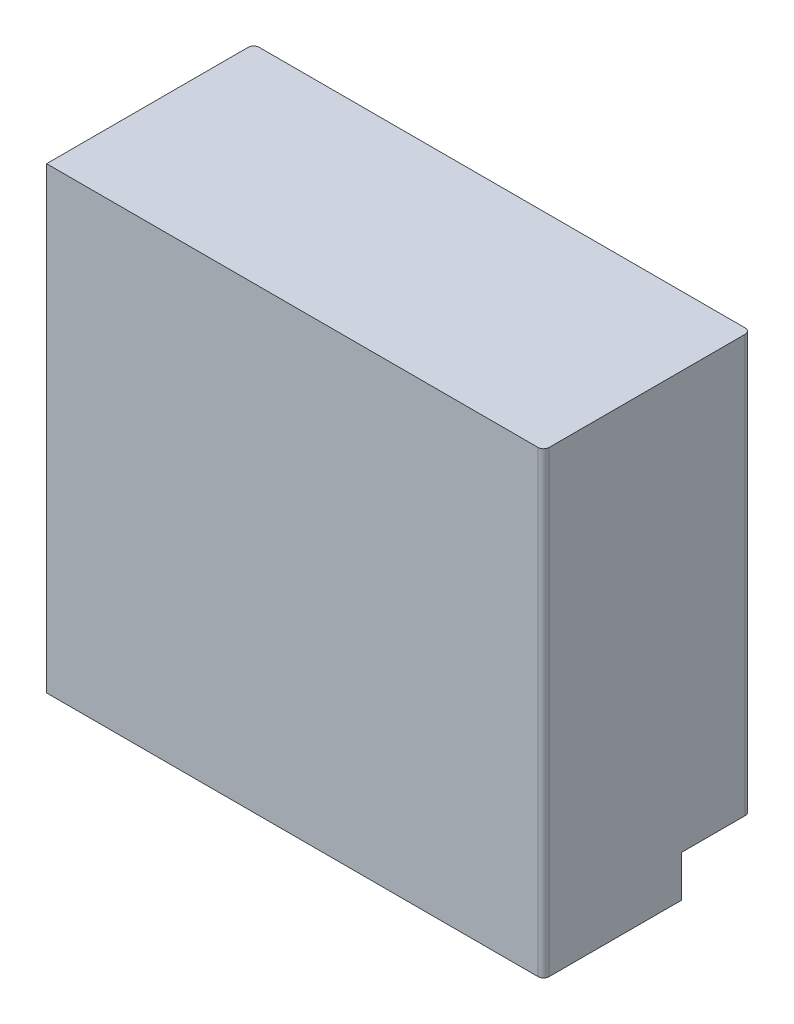
SolidWorks part; units mm, degrees
ref_plane "Front Plane" through (0, 0, 0) normal (0, 0, 1) x (1, 0, 0)
ref_plane "Top Plane" through (0, 0, 0) normal (0, 1, 0) x (1, 0, 0)
ref_plane "Right Plane" through (0, 0, 0) normal (1, 0, 0) x (0, 0, -1)
sketch "Sketch1" plane through (0, 0, 0) normal (0, 1, 0) x (1, 0, 0)
  line L0 (0, 37.7318) -> (0, -34.3847) construction
  line L1 (-55.0763, 0) -> (61.9228, 0) construction
  line L3 (90, 37.5) -> (-90, 37.5)
  line L4 (90, 37.5) -> (90, -37.5)
  line L5 (90, -37.5) -> (-90, -37.5)
  line L6 (-90, 37.5) -> (-90, -37.5)
  line L7 (90, 37.5) -> (-90, -37.5) construction
  line L8 (90, -37.5) -> (-90, 37.5) construction
  point P4 (0, 0)
  dimension "D1" = 75
  dimension "D2" = 180
extrude "Boss-Extrude1" add sketch "Sketch1" along normal blind 166
sketch "Sketch2" plane through (0, 0, 0) normal (0, -1, 0) x (1, 0, 0)
  line L0 (0, 67.883) -> (0, -86.2061) construction
  line L1 (-90, -37.5) -> (-40, -37.5)
  line L2 (-90, -37.5) -> (-90, -12.5)
  line L3 (-90, -12.5) -> (-40, -12.5)
  line L4 (-40, -37.5) -> (-40, -12.5)
  line L5 (90, -37.5) -> (90, -12.5)
  line L6 (90, -37.5) -> (40, -37.5)
  line L7 (40, -37.5) -> (40, -12.5)
  line L8 (90, -12.5) -> (40, -12.5)
  dimension "D1" = 25
  dimension "D2" = 50
extrude "Cut-Extrude1" cut sketch "Sketch2" against normal blind 15
fillet "Fillet1" radius 2 4 edges at (0, 0, -37.5) (-90, 90.5, -37.5) (90, 90.5, -37.5) (90, 83, 37.5)
sketch "Sketch3" plane through (0, 15, 0) normal (0, -1, 0) x (1, 0, 0)
  line L0 (0, 38.4115) -> (0, -46.7096) construction
  line L1 (-88, -37.5) -> (-40, -37.5) construction
  line L2 (-74, -17.5) -> (-70, -17.5)
  line L3 (-74, -17.5) -> (-74, -32.5)
  line L4 (-74, -32.5) -> (-70, -32.5)
  line L5 (-70, -17.5) -> (-70, -32.5)
  line L6 (74, -32.5) -> (70, -32.5)
  line L7 (74, -17.5) -> (70, -17.5)
  line L8 (70, -17.5) -> (70, -32.5)
  line L9 (74, -17.5) -> (74, -32.5)
  dimension "D1" = 5
  dimension "D2" = 70
  dimension "D3" = 4
  dimension "D4" = 15
extrude "Boss-Extrude2" add sketch "Sketch3" along normal blind 14
fillet "Fillet2" radius 4 4 edges at (72, 1, -32.5) (72, 1, -17.5) (-72, 1, -17.5) (-72, 1, -32.5)
